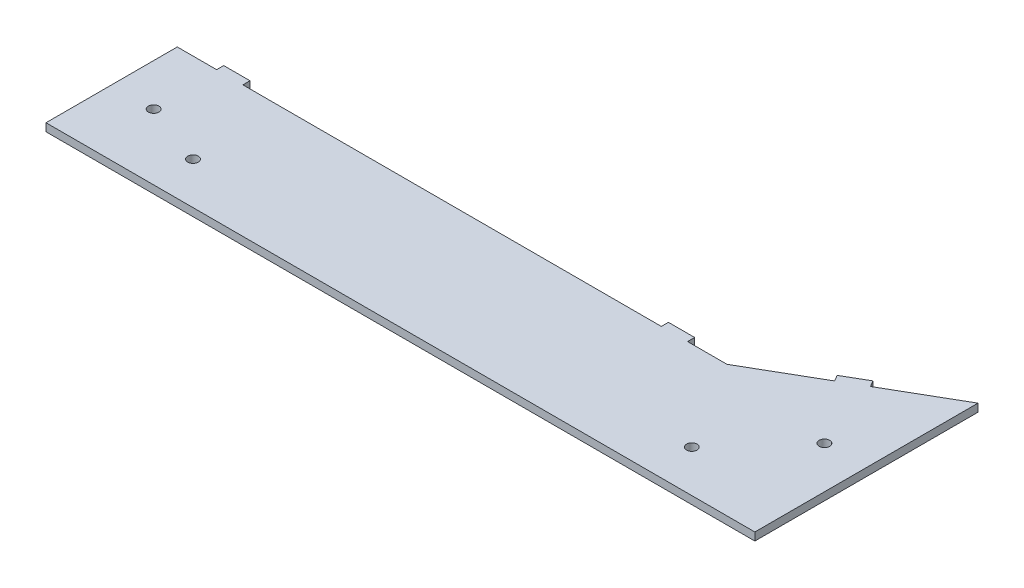
SolidWorks part; units mm, degrees
ref_plane "Front" through (0, 0, 0) normal (0, 0, 1) x (1, 0, 0)
ref_plane "Top" through (0, 0, 0) normal (0, 1, 0) x (1, 0, 0)
ref_plane "Right" through (0, 0, 0) normal (1, 0, 0) x (0, 0, -1)
sketch "Sketch1" plane through (0, 0, 0) normal (0, 1, 0) x (1, 0, 0)
  line L0 (101.1243, 11.2137) -> (101.1243, 66.2733)
  line L1 (40.5025, 31.2733) -> (-168.8757, 31.2733)
  line L2 (101.1243, 11.2137) -> (101.1243, -18.7267)
  line L3 (101.1243, -18.7267) -> (-168.8757, -18.7267)
  line L4 (-168.8757, 31.2733) -> (-168.8757, -18.7267)
  line L5 (101.1243, 11.2137) -> (-168.8757, -18.7267) construction
  line L6 (101.1243, -18.7267) -> (-168.8757, 31.2733) construction
  line L7 (101.1243, 66.2733) -> (40.5025, 31.2733)
  point P0 (0, 0)
  dimension "D1" = 50
  dimension "D2" = 270
  dimension "D3" = 70
  dimension "D4" = 30
  dimension "D5" = 40.5025
extrude "Boss-Extrude1" add sketch "Sketch1" along normal blind 3 contours L1 L4 L3 L2 L0 L7
sketch "Sketch2" plane through (0, 3, 0) normal (0, 1, 0) x (1, 0, 0)
  line L0 (-168.8757, 31.2733) -> (-168.8757, -18.7267) construction
  line L2 (101.1243, 66.2733) -> (101.1243, -18.7267) construction
  circle A0 centre (-152.8757, 6.2733) radius 2
  circle A1 centre (85.1243, 23.7733) radius 2
  point P5 (-168.8757, 6.2733)
  point P9 (101.1243, 23.7733)
  dimension "D1" = 4
  dimension "D3" = 4
  dimension "D2" = 16
  dimension "D4" = 16
extrude "Cut-Extrude1" cut sketch "Sketch2" against normal up to next
sketch "Sketch3" plane through (0, 3, 0) normal (0, 1, 0) x (1, 0, 0)
  line L0 (101.1243, -18.7267) -> (-168.8757, -18.7267) construction
  line L2 (-168.8757, 31.2733) -> (-168.8757, -18.7267) construction
  line L3 (101.1243, 66.2733) -> (101.1243, -18.7267) construction
  circle A0 centre (-128.8757, -2.7267) radius 2
  circle A1 centre (61.1243, -2.7267) radius 2
  dimension "D1" = 4
  dimension "D4" = 4
  dimension "D2" = 40
  dimension "D3" = 16
  dimension "D5" = 16
  dimension "D6" = 40
extrude "Cut-Extrude2" cut sketch "Sketch3" against normal up to next
sketch "Sketch4" plane through (0, 0, -31.2733) normal (0, 0, 1) x (1, 0, 0)
  line L0 (40.5025, 3) -> (-168.8757, 3) construction
  line L1 (-143.8757, 3) -> (-153.8757, 3)
  line L2 (-143.8757, 3) -> (-143.8757, 0)
  line L3 (-143.8757, 0) -> (-153.8757, 0)
  line L4 (-153.8757, 3) -> (-153.8757, 0)
  line L5 (40.5025, 0) -> (-168.8757, 0) construction
  line L6 (-168.8757, 3) -> (-168.8757, 0) construction
  line L7 (25.5025, 3) -> (15.5025, 3)
  line L8 (25.5025, 3) -> (25.5025, 0)
  line L9 (25.5025, 0) -> (15.5025, 0)
  line L10 (15.5025, 3) -> (15.5025, 0)
  line L12 (40.5025, 3) -> (40.5025, 0) construction
  point P14 (-168.8757, 1.5)
  point P17 (40.5025, 1.5)
  dimension "D1" = 10
  dimension "D2" = 10
  dimension "D3" = 15
  dimension "D4" = 15
extrude "Boss-Extrude3" add sketch "Sketch4" against normal blind 2.7
sketch "Sketch5" plane through (-3.4161, 0, -5.9168) normal (-0.5, 0, -0.866) x (-0.866, 0, 0.5)
  line L0 (-120.7129, 3) -> (-50.7129, 3) construction
  line L1 (-90.7129, 3) -> (-80.7129, 3)
  line L2 (-90.7129, 3) -> (-90.7129, 0)
  line L3 (-90.7129, 0) -> (-80.7129, 0)
  line L4 (-80.7129, 3) -> (-80.7129, 0)
  line L5 (-120.7129, 0) -> (-50.7129, 0) construction
  point P8 (-85.7129, 3)
  point P9 (-85.7129, 3)
  dimension "D1" = 10
extrude "Boss-Extrude4" add sketch "Sketch5" along normal blind 2.7
